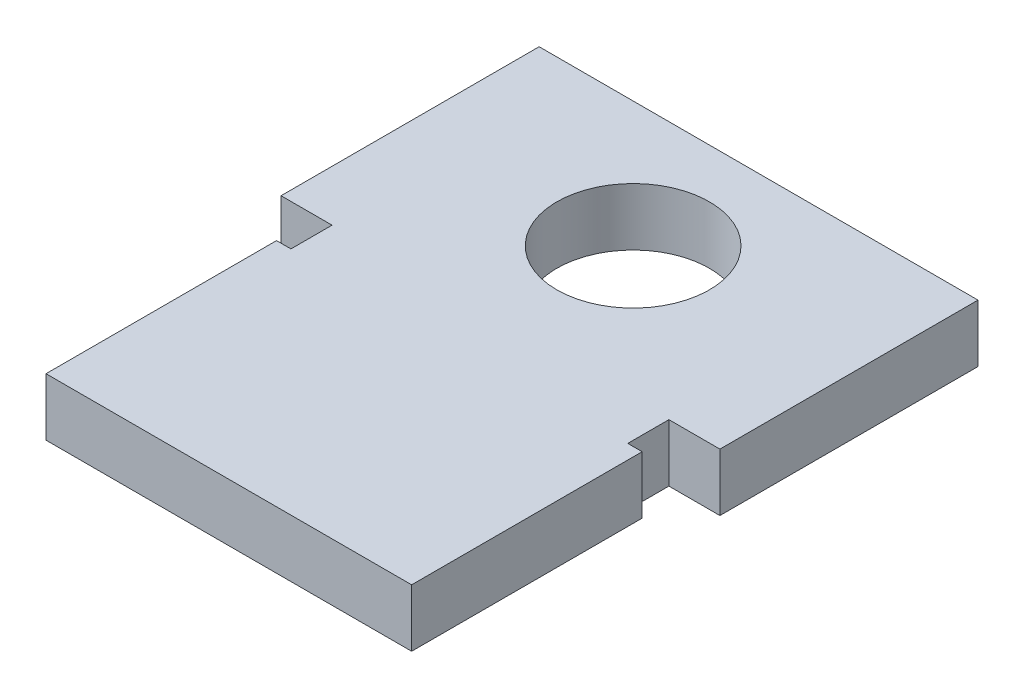
SolidWorks part; units mm, degrees
material "1060-H16"
ref_plane "Front Plane" through (0, 0, 0) normal (0, 0, 1) x (1, 0, 0)
ref_plane "Top Plane" through (0, 0, 0) normal (0, 1, 0) x (1, 0, 0)
ref_plane "Right Plane" through (0, 0, 0) normal (1, 0, 0) x (0, 0, -1)
sketch "Sketch1" plane through (0, 0, 0) normal (0, 1, 0) x (1, 0, 0)
  line L1 (-5.335, 3.05) -> (5.335, 3.05)
  line L2 (-5.335, 3.05) -> (-5.335, -9.83)
  line L3 (-5.335, -9.83) -> (5.335, -9.83)
  line L4 (5.335, 3.05) -> (5.335, -9.83)
  circle A0 centre (0, 0) radius 1.855
  point P4 (0, 3.05)
  dimension "D4" = 3.71
  dimension "D1" = 10.67
  dimension "D2" = 12.88
  dimension "D3" = 3.05
extrude "Boss-Extrude1" add sketch "Sketch1" along normal blind 1.4
sketch "Sketch2" plane through (0, 1.4, 0) normal (0, 1, 0) x (1, 0, 0)
  line L0 (5.335, 3.05) -> (-5.335, 3.05) construction
  line L1 (-5.335, -9.83) -> (-4.445, -9.83)
  line L2 (-5.335, -9.83) -> (-5.335, -3.225)
  line L3 (-5.335, -3.225) -> (-4.445, -3.225)
  line L4 (-4.445, -9.83) -> (-4.445, -3.225)
  dimension "D1" = 0.89
  dimension "D2" = 6.275
extrude "Cut-Extrude1" cut sketch "Sketch2" against normal through all
mirror "Mirror1" about plane through (0, 0, 0) normal (1, 0, 0) of "Cut-Extrude1"
sketch "Sketch3" plane through (0, 1.4, 0) normal (0, 1, 0) x (1, 0, 0)
  line L1 (-4.445, -3.225) -> (-4.095, -3.225)
  line L2 (-4.445, -3.225) -> (-4.445, -4.225)
  line L3 (-4.445, -4.225) -> (-4.095, -4.225)
  line L4 (-4.095, -3.225) -> (-4.095, -4.225)
  dimension "D1" = 0.35
  dimension "D2" = 1
extrude "Cut-Extrude2" cut sketch "Sketch3" against normal through all
mirror "Mirror2" about plane through (0, 0, 0) normal (1, 0, 0) of "Cut-Extrude2"
